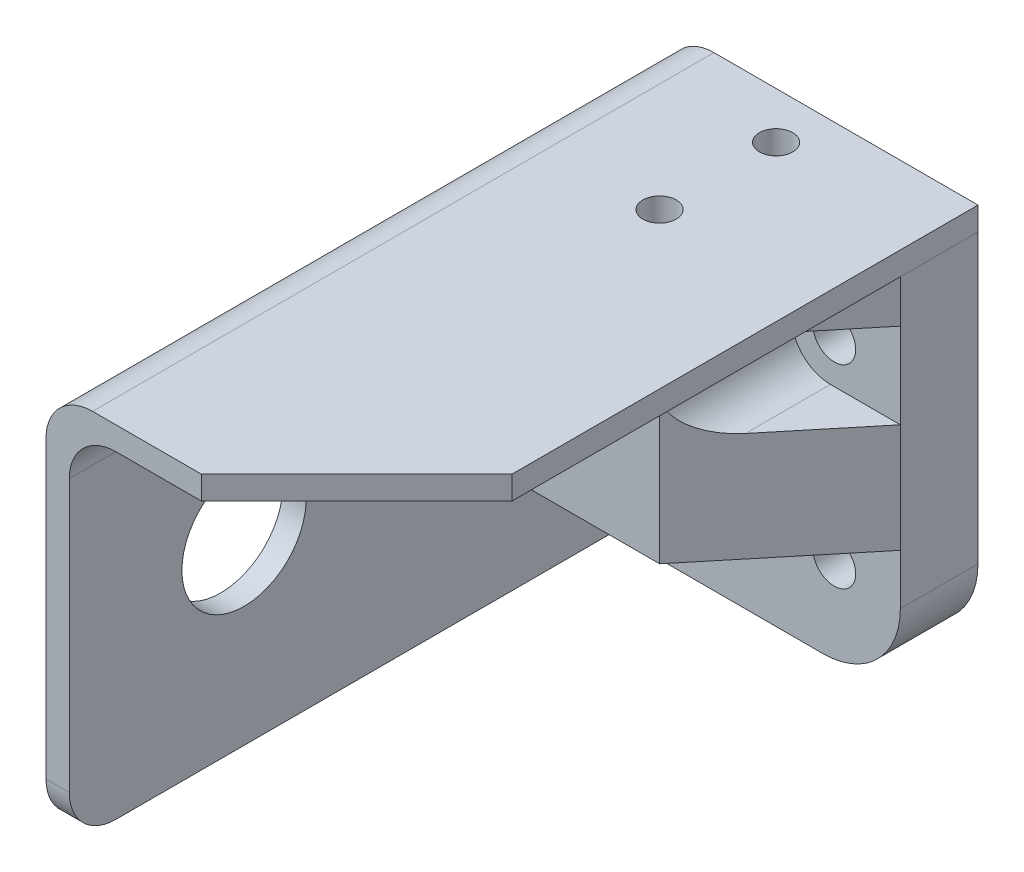
SolidWorks part; units mm, degrees
ref_plane "Front Plane" through (0, 0, 0) normal (0, 0, 1) x (1, 0, 0)
ref_plane "Top Plane" through (0, 0, 0) normal (0, 1, 0) x (1, 0, 0)
ref_plane "Right Plane" through (0, 0, 0) normal (1, 0, 0) x (0, 0, -1)
sketch "Sketch1" plane through (0, 0, 0) normal (0, 0, 1) x (1, 0, 0)
  line L0 (0, 0) -> (0, 50)
  line L1 (0, 50) -> (40, 50)
  dimension "D1" = 50
  dimension "D2" = 40
extrude "Extrude-Thin1" add sketch "Sketch1" along normal blind 80 thin
sketch "Sketch2" plane through (0, 0, 0) normal (-1, 0, 0) x (0, 0, 1)
  line L0 (57.5, 23.5) -> (0, 23.5) construction
  line L1 (0, 0) -> (0, 50) construction
  line L2 (80, 0) -> (80, 47) construction
  line L3 (80, 0) -> (80, 47)
  line L4 (0, 0) -> (0, 47) construction
  line L5 (0, 0) -> (0, 47)
  circle A0 centre (57.5, 23.5) radius 8
  dimension "D1" = 16
  dimension "D2" = 57.5
extrude "Cut-Extrude1" cut sketch "Sketch2" against normal blind 10
fillet "Fillet1" radius 6 3 edges at (3, 47, 40) (0, 50, 40) (1.5, 0, 80)
chamfer "Chamfer1" distance 20 angle 45 1 edges at (40, 48.5, 80)
sketch "Sketch3" plane through (0, 0, 0) normal (0, 0, -1) x (-1, 0, 0)
  line L0 (-40, 47) -> (-40, 0)
  line L1 (-40, 0) -> (-3, 0)
  line L2 (-40, 47) -> (-3, 47)
  line L3 (-3, 47) -> (-3, 0)
  line L4 (-21.5, 47) -> (-21.5, 0) construction
  line L5 (-40, 23.5) -> (-3, 23.5) construction
  line L7 (-31.5, 36) -> (-11.5, 36) construction
  line L8 (-31.5, 36) -> (-31.5, 11) construction
  line L9 (-31.5, 11) -> (-11.5, 11) construction
  line L10 (-11.5, 36) -> (-11.5, 11) construction
  line L11 (-31.5, 36) -> (-11.5, 11) construction
  line L12 (-31.5, 11) -> (-11.5, 36) construction
  arc A0 (-3, 41) -> (-9, 47) centre (-9, 41) ccw construction
  arc A1 (-3, 41) -> (-9, 47) centre (-9, 41) ccw
  circle A2 centre (-31.5, 11) radius 2.75
  circle A3 centre (-11.5, 11) radius 2.75
  circle A4 centre (-11.5, 36) radius 2.75
  circle A5 centre (-31.5, 36) radius 2.75
  point P15 (-21.5, 23.5)
  line M19 (-40, 47) -> (-9, 47)
  arc M20 (-9, 47) -> (-3, 41) centre (-9, 41) cw
  line M21 (-3, 41) -> (-3, 0)
  dimension "D1" = 5.5
  dimension "D2" = 20
  dimension "D3" = 25
extrude "Boss-Extrude1" add sketch "Sketch3" against normal blind 27 separate body contours L0 L1 A5 A4 A3 A2 M21 M20 M19
sketch "Sketch4" plane through (0, 0, 0) normal (-1, 0, 0) x (0, 0, 1)
  line L1 (27, 50) -> (27, 0) construction
  line L2 (0, 25) -> (27, 25) construction
  line L7 (13.5, 25) -> (13.5, 0) construction
  line L8 (74, 0) -> (0, 0) construction
  line L10 (0, 50) -> (80, 50) construction
  line L11 (0, 0) -> (0, 44) construction
  line L12 (27, 41) -> (27, 0) construction
  circle A0 centre (7, 25) radius 2.15
  circle A1 centre (20, 25) radius 2.15
  dimension "D1" = 4.3
  dimension "D2" = 13
extrude "Cut-Extrude2" cut sketch "Sketch4" against normal blind 22
sketch "Sketch5" plane through (0, 0, 27) normal (0, 0, 1) x (1, 0, 0)
  line L0 (6, 16.5) -> (40, 16.5)
  line L2 (26, 41.5) -> (26, 30.5)
  line L4 (26, 41.5) -> (40, 41.5)
  line L5 (40, 47) -> (40, 0) construction
  line L7 (6, 16.5) -> (6, 0)
  line L8 (40, 0) -> (3, 0) construction
  line L9 (6, 0) -> (40, 0)
  line L11 (26, 30.5) -> (40, 30.5)
  line L12 (40, 30.5) -> (40, 41.5)
  line L13 (40, 16.5) -> (40, 0)
  circle A0 centre (11.5, 36) radius 5.5
  circle A5 centre (31.5, 36) radius 5.5 construction
  circle A6 centre (11.5, 11) radius 5.5 construction
  dimension "D1" = 11
extrude "Cut-Extrude3" cut sketch "Sketch5" against normal blind 17
sketch "Sketch6" plane through (0, 50, 0) normal (0, 1, 0) x (1, 0, 0)
  line L0 (20, -27) -> (20, 0) construction
  line L4 (40, -27) -> (9, -27) construction
  line L5 (40, -27) -> (0, -27) construction
  line L7 (6, 0) -> (40, 0) construction
  line L8 (20, -13.5) -> (40, -13.5) construction
  line L9 (40, -60) -> (40, 0) construction
  line L10 (0, -80) -> (0, 0) construction
  circle A0 centre (20, -6) radius 2.15
  circle A1 centre (20, -21) radius 2.15
  dimension "D1" = 4.3
  dimension "D2" = 15
extrude "Cut-Extrude4" cut sketch "Sketch6" against normal blind 21
sketch "Sketch7" plane through (0, 41.5, 0) normal (0, -1, 0) x (1, 0, 0)
  line L0 (26, 27) -> (40, 10)
  line L1 (40, 10) -> (40, 27) construction
  line L2 (40, 27) -> (26, 27) construction
  line L3 (40, 10) -> (40, 27)
  line L4 (40, 27) -> (26, 27)
extrude "Cut-Extrude5" cut sketch "Sketch7" against normal up to surface (5.5 mm away) and the other way through all up to face at (20, 47, 8.15)
sketch "Sketch8" plane through (6, 0, 0) normal (1, 0, 0) x (0, 0, -1)
  line L0 (-27, 16.5) -> (-10, 0)
  line L1 (-10, 16.5) -> (-10, 0) construction
  line L2 (-10, 0) -> (-10, 16.5) construction
  line L3 (-10, 0) -> (-27, 0)
  line L4 (-10, 0) -> (-27, 0) construction
  line L5 (-27, 16.5) -> (-27, 0) construction
  line L6 (-27, 0) -> (-27, 16.5)
extrude "Cut-Extrude6" cut sketch "Sketch8" against normal up to surface (3 mm away) up to face at (3, 25, 9.15)
fillet "Fillet6" radius 10 1 edges at (40, 0, 5)
fillet "Fillet7" radius 5 3 edges at (26, 41.5, 18.5) (6, 16.5, 18.5) (26, 30.5, 18.5)
